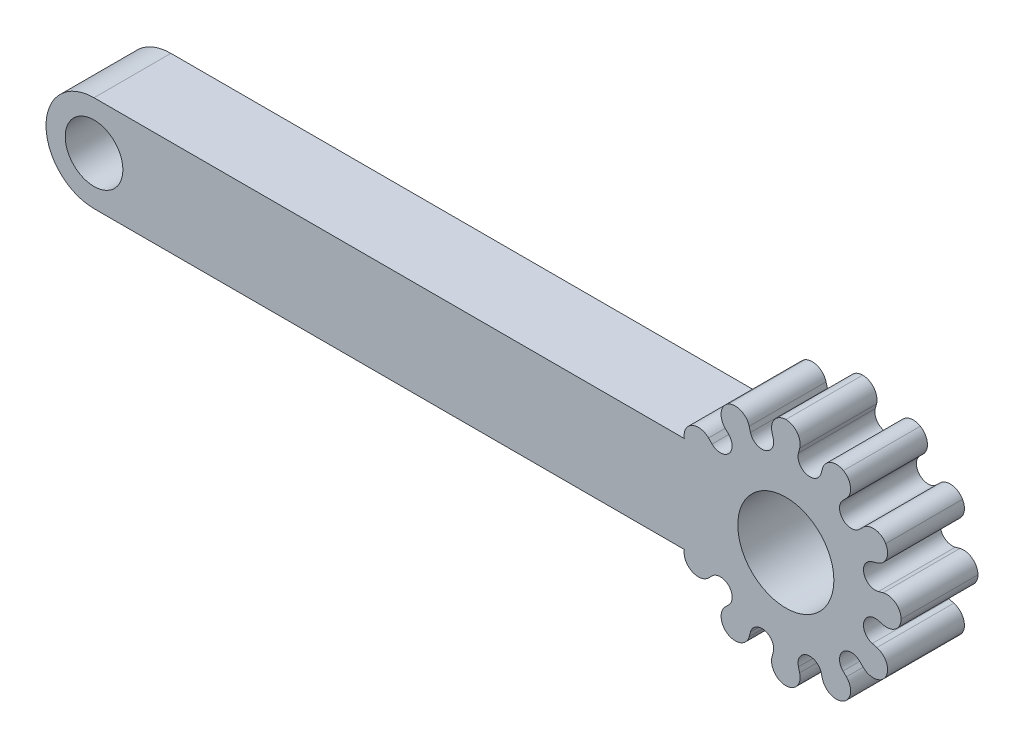
SolidWorks part; units mm, degrees
ref_plane "Front Plane" through (0, 0, 0) normal (0, 0, 1) x (1, 0, 0)
ref_plane "Top Plane" through (0, 0, 0) normal (0, 1, 0) x (1, 0, 0)
ref_plane "Right Plane" through (0, 0, 0) normal (1, 0, 0) x (0, 0, -1)
sketch "Sketch1" plane through (0, 0, 0) normal (0, 0, 1) x (1, 0, 0)
  line L0 (-18, 0) -> (18, 0) construction
  line L1 (-18, 0) -> (-18, -2.5) construction
  line L2 (-18, 0) -> (-18, 2.5) construction
  line L3 (-18, 2.5) -> (12.5456, 2.5)
  line L4 (-18, -2.5) -> (12.5456, -2.5)
  circle A0 centre (-18, 0) radius 1.5
  arc A1 (-18, 2.5) -> (-18, -2.5) centre (-18, 0) ccw
  arc A2 (12.5456, -2.5) -> (12.5456, 2.5) centre (18, 0) ccw
  point P4 (0, 0)
  dimension "D2" = 3
  dimension "D3" = 5
  dimension "D4" = 12
  dimension "D1" = 36
extrude "Boss-Extrude1" add sketch "Sketch1" along normal blind 4
sketch "Sketch2" plane through (0, 0, 4) normal (0, 0, 1) x (1, 0, 0)
  line L0 (18, 6) -> (18, -6) construction
  line L1 (18, 0) -> (21, 5.1962) construction
  line L2 (18, 0) -> (19.2475, 4.6558) construction
  line L3 (18.72, 5.06) -> (18.653, 4.81)
  line L4 (18.653, 4.81) -> (19.842, 4.5015) construction
  line L5 (19.842, 4.5015) -> (19.9065, 4.7421)
  arc A0 (12.5456, -2.5) -> (12.5456, 2.5) centre (18, 0) ccw construction
  arc A1 (18, 6) -> (18.72, 5.06) centre (17.9945, 5.25) cw
  arc A2 (18.653, 4.81) -> (19.842, 4.5015) centre (19.2475, 4.6558) ccw
  arc A3 (21, 5.1962) -> (19.9065, 4.7421) centre (20.6298, 4.5439) ccw
  arc A5 (18, 6) -> (21, 5.1962) centre (18.8612, 3.214) cw
  dimension "D6" = 0.75
  dimension "D1" = 30
  dimension "D2" = 4.82
  dimension "D3" = 15
  dimension "D4" = 0.94
  dimension "D5" = 0.72
  dimension "D8" = 0.25
extrude "Cut-Extrude2" cut sketch "Sketch2" against normal through all
pattern_circular "CirPattern1" count 12 over 360 about axis through (18, 0, 0) along (0, 0, 1) of "Cut-Extrude2"
sketch "Sketch3" plane through (0, 0, 4) normal (0, 0, 1) x (1, 0, 0)
  line L0 (12.374, 2.5) -> (-18, 2.5) construction
  line L1 (8.0978, 2.5) -> (15.9609, 2.5)
  line L2 (8.0978, 2.5) -> (8.0978, -2.5)
  line L3 (8.0978, -2.5) -> (15.9609, -2.5)
  line L4 (15.9609, 2.5) -> (15.9609, -2.5)
  line L5 (-18, -2.5) -> (12.374, -2.5) construction
extrude "Boss-Extrude2" add sketch "Sketch3" against normal blind 4
sketch "Sketch4" plane through (0, 0, 4) normal (0, 0, 1) x (1, 0, 0)
  line L0 (18, 6) -> (18, -6) construction
  circle A0 centre (18, 0) radius 2.5
  dimension "D1" = 5
extrude "Cut-Extrude3" cut sketch "Sketch4" against normal through all
